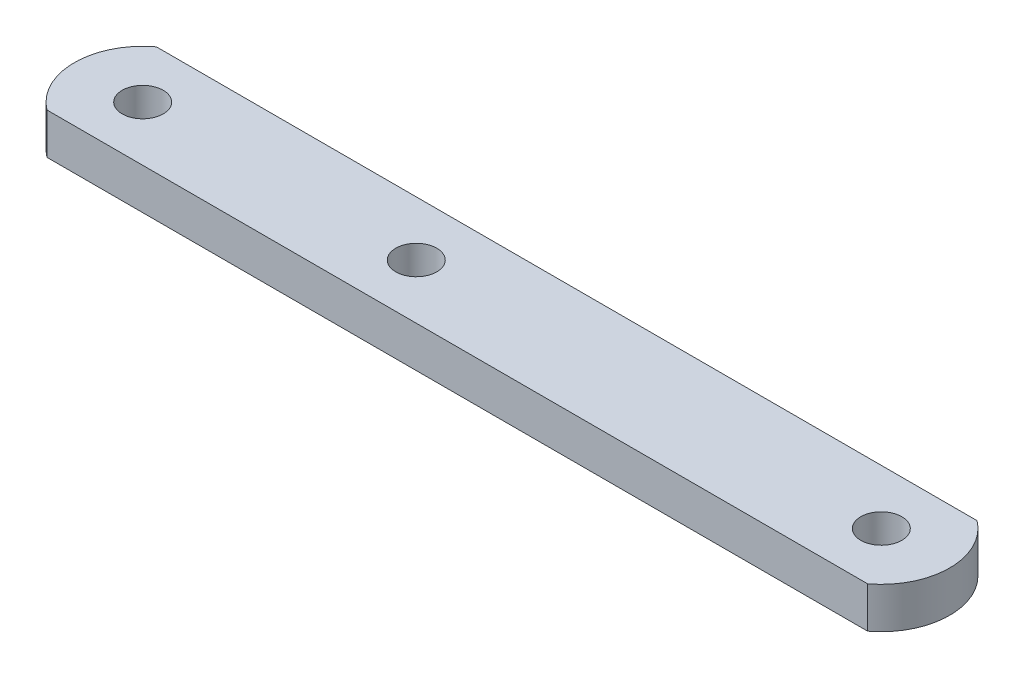
SolidWorks part; units mm, degrees
ref_plane "Front Plane" through (0, 0, 0) normal (0, 0, 1) x (1, 0, 0)
ref_plane "Top Plane" through (0, 0, 0) normal (0, 1, 0) x (1, 0, 0)
ref_plane "Right Plane" through (0, 0, 0) normal (1, 0, 0) x (0, 0, -1)
sketch "Sketch1" plane through (0, 0, 0) normal (0, 1, 0) x (1, 0, 0)
  line L0 (-30, 8) -> (-30, 0) construction
  line L1 (0, 0) -> (-60, 0)
  line L3 (0, 8) -> (-60, 8)
  arc A0 (-60, 8) -> (-60, 0) centre (-57, 4) ccw
  arc A1 (0, 8) -> (0, 0) centre (-3, 4) cw
  circle A2 centre (-57, 4) radius 1.5
  circle A3 centre (-3, 4) radius 1.5
  circle A4 centre (-37, 4) radius 1.5
  dimension "D3" = 10
  dimension "D4" = 3
  dimension "D5" = 3
  dimension "D1" = 8
  dimension "D2" = 60
  dimension "D6" = 20
extrude "Boss-Extrude1" add sketch "Sketch1" along normal blind 3
